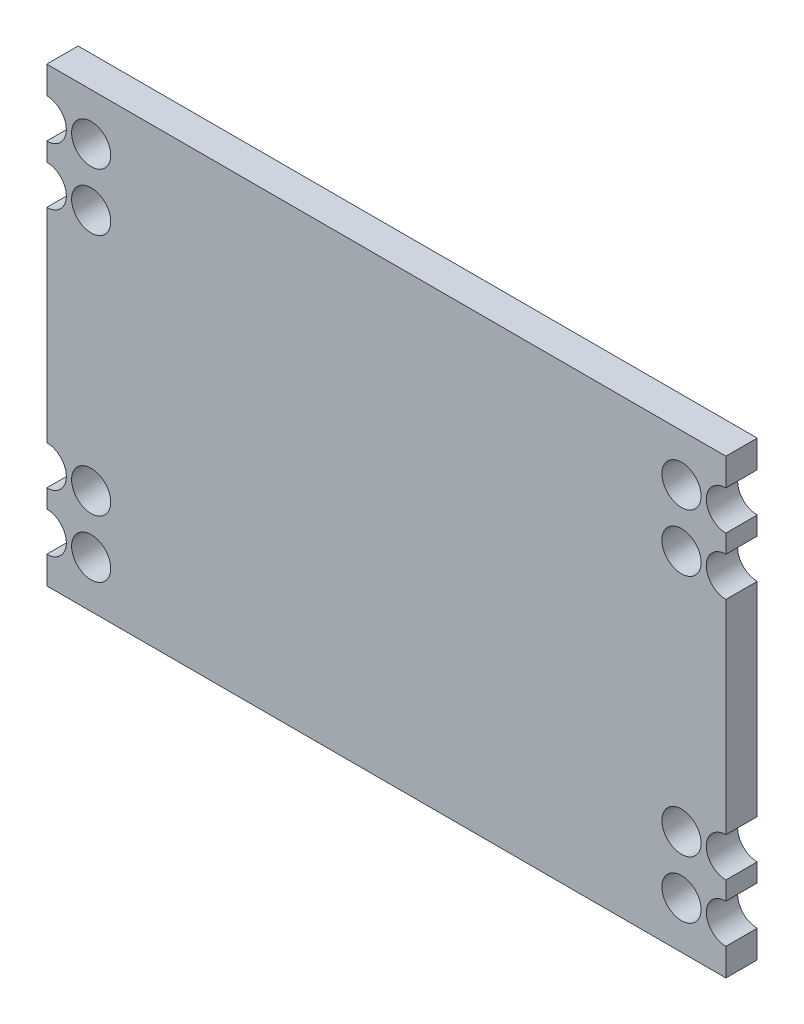
SolidWorks part; units mm, degrees
ref_plane "Front Plane" through (0, 0, 0) normal (0, 0, 1) x (1, 0, 0)
ref_plane "Top Plane" through (0, 0, 0) normal (0, 1, 0) x (1, 0, 0)
ref_plane "Right Plane" through (0, 0, 0) normal (1, 0, 0) x (0, 0, -1)
sketch "Sketch1" plane through (0, 0, 0) normal (0, 0, 1) x (1, 0, 0)
  line L0 (0, 8.65) -> (0, -8.65) construction
  line L1 (-13, 8.65) -> (13, 8.65)
  line L2 (-13, 8.65) -> (-13, -8.65)
  line L3 (-13, -8.65) -> (13, -8.65)
  line L4 (13, 8.65) -> (13, -8.65)
  line L5 (-13, 8.65) -> (13, -8.65) construction
  line L6 (-13, -8.65) -> (13, 8.65) construction
  line L7 (-13, 0) -> (13, 0) construction
  circle A0 centre (-13, 6.85) radius 0.75
  circle A1 centre (-11.3, 6.85) radius 0.75
  circle A2 centre (-13, 4.65) radius 0.75
  circle A3 centre (-11.3, 4.65) radius 0.75
  circle A4 centre (-13, -6.85) radius 0.75
  circle A5 centre (-13, -4.65) radius 0.75
  circle A6 centre (-11.3, -4.65) radius 0.75
  circle A7 centre (-11.3, -6.85) radius 0.75
  circle A8 centre (11.3, -6.85) radius 0.75
  circle A9 centre (11.3, -4.65) radius 0.75
  circle A10 centre (13, -6.85) radius 0.75
  circle A11 centre (13, -4.65) radius 0.75
  circle A12 centre (13, 6.85) radius 0.75
  circle A13 centre (13, 4.65) radius 0.75
  circle A14 centre (11.3, 6.85) radius 0.75
  circle A15 centre (11.3, 4.65) radius 0.75
  point P0 (0, 0)
  point P10 (-13, 7.85)
  point P11 (-13, 6.85)
  point P12 (-13, 148.7424)
  point P13 (-13, 141.9273)
  dimension "D3" = 1.5
  dimension "D4" = 1.7
  dimension "D7" = 1.5
  dimension "D9" = 2.2
  dimension "D1" = 0.8
  dimension "D2" = 1
  dimension "D5" = 17.3
  dimension "D6" = 26
  dimension "D8" = 2.2
extrude "Boss-Extrude1" add sketch "Sketch1" along normal blind 1.2 contours L4 A13 A12 L1 L2 A0 A2 A5 A4 L3 A10 A11 A14 A9 A8 A6 A3 A1 A7 A15
